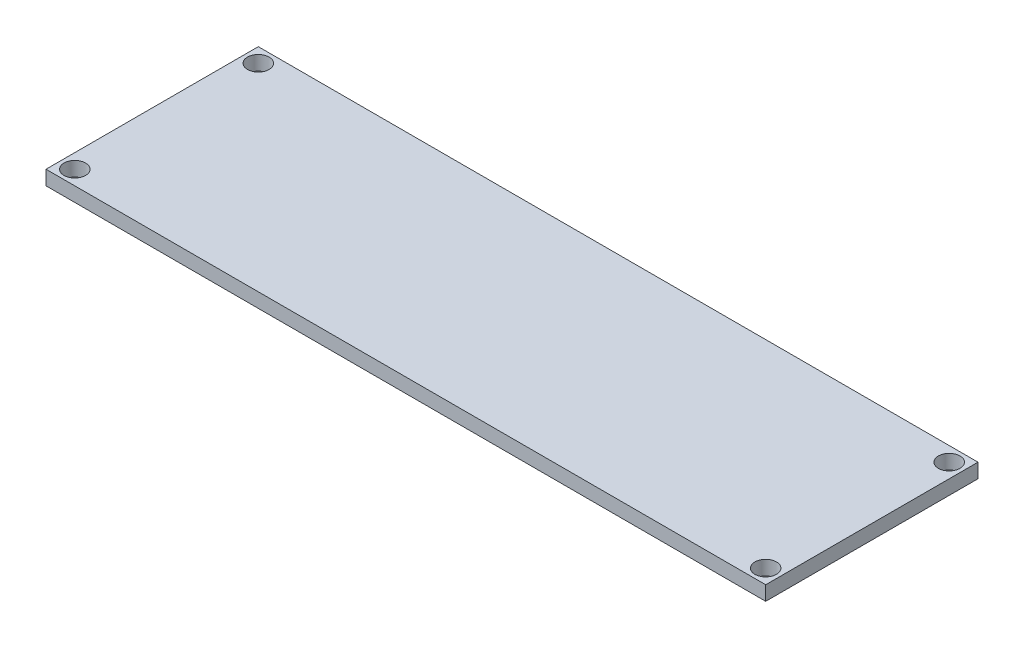
SolidWorks part; units mm, degrees
ref_plane "Front" through (0, 0, 0) normal (0, 0, 1) x (1, 0, 0)
ref_plane "Top" through (0, 0, 0) normal (0, 1, 0) x (1, 0, 0)
ref_plane "Right" through (0, 0, 0) normal (1, 0, 0) x (0, 0, -1)
sketch "Sketch1" plane through (0, 0, 0) normal (0, 1, 0) x (1, 0, 0)
  line L1 (-40.0267, 17.0192) -> (59.9733, 17.0192)
  line L2 (-40.0267, 17.0192) -> (-40.0267, -12.4808)
  line L3 (-40.0267, -12.4808) -> (59.9733, -12.4808)
  line L4 (59.9733, 17.0192) -> (59.9733, -12.4808)
  dimension "D1" = 100
  dimension "D2" = 29.5
extrude "Boss-Extrude1" add sketch "Sketch1" along normal blind 2
sketch "Sketch2" plane through (0, 2, 0) normal (0, 1, 0) x (1, 0, 0)
  line L0 (-40.0267, 17.0192) -> (-40.0267, -12.4808) construction
  line L1 (59.9733, 17.0192) -> (-40.0267, 17.0192) construction
  line L2 (-40.0267, -12.4808) -> (59.9733, -12.4808) construction
  line L3 (59.9733, -12.4808) -> (59.9733, 17.0192) construction
  circle A0 centre (57.9733, -10.4808) radius 1.5
  circle A1 centre (-38.0267, -10.4808) radius 1.5
  circle A2 centre (-38.0267, 15.0192) radius 1.5
  circle A3 centre (57.9733, 15.0192) radius 1.5
  dimension "D1" = 3
  dimension "D2" = 3
  dimension "D3" = 3
  dimension "D4" = 3
  dimension "D5" = 2
  dimension "D6" = 2
  dimension "D7" = 2
  dimension "D8" = 2
  dimension "D9" = 2
  dimension "D10" = 2
  dimension "D11" = 2
  dimension "D12" = 2
extrude "Cut-Extrude1" cut sketch "Sketch2" against normal up to surface (2 mm away) up to face at (9.9733, 0, -2.2692)
